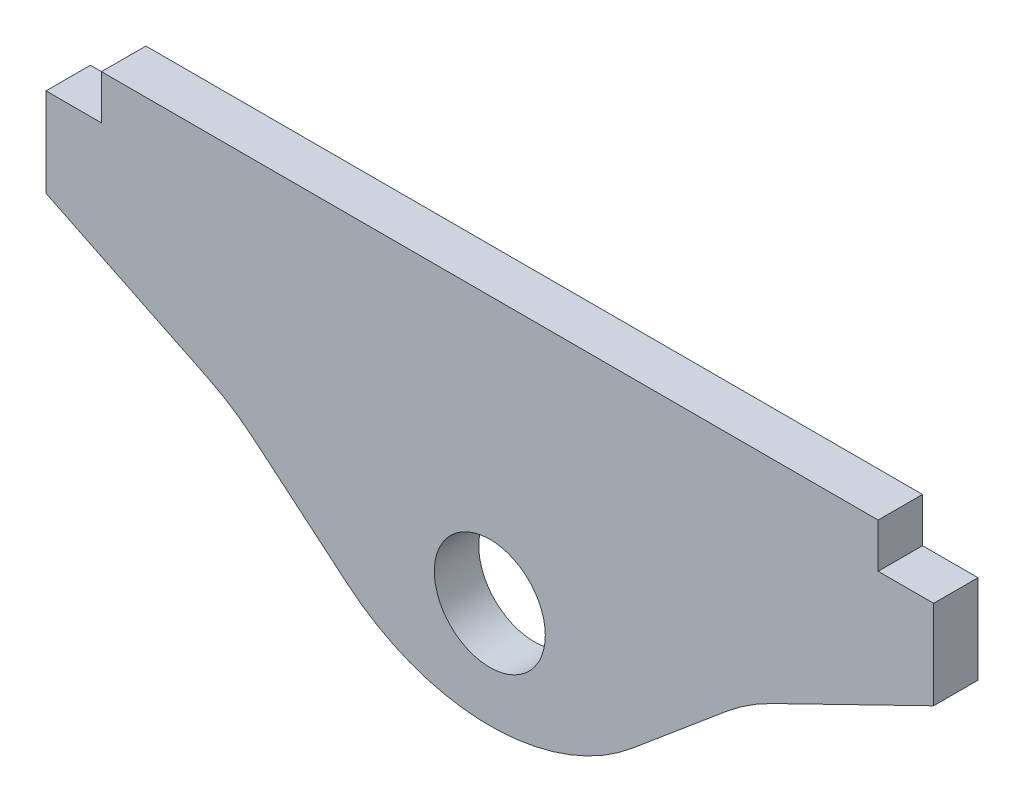
SolidWorks part; units mm, degrees
material "ﾊﾞﾙｻ"
ref_plane "正面" through (0, 0, 0) normal (0, 0, 1) x (1, 0, 0)
ref_plane "平面" through (0, 0, 0) normal (0, 1, 0) x (1, 0, 0)
ref_plane "右側面" through (0, 0, 0) normal (1, 0, 0) x (0, 0, -1)
sketch "ｽｹｯﾁ1" plane through (0, 0, 0) normal (0, 0, 1) x (1, 0, 0)
  line L0 (0, 0) -> (0, 38.4947) construction
  line L1 (0, -7.8324) -> (11.6055, 1.9057)
  line L2 (11.6055, 1.9057) -> (20, 6)
  line L3 (-11.6055, 1.9057) -> (-20, 6)
  line L4 (0, -7.8324) -> (-11.6055, 1.9057)
  line L5 (20, 6) -> (-20, 6)
  line L6 (-20, 6) -> (-20, 10)
  line L7 (-20, 10) -> (-17.5, 10)
  line L8 (-17.5, 10) -> (-17.5, 12)
  line L9 (-17.5, 12) -> (17.5, 12)
  line L10 (20, 10) -> (17.5, 10)
  line L11 (20, 6) -> (20, 10)
  line L12 (17.5, 10) -> (17.5, 12)
  circle A0 centre (0, 0) radius 2.5
  point P8 (0, 6)
  point P16 (0, 12)
  dimension "D3" = 5
  dimension "D1" = 50
  dimension "D2" = 6
  dimension "D4" = 6
  dimension "D5" = 20
  dimension "D6" = 26
  dimension "D7" = 4
  dimension "D8" = 2
  dimension "D9" = 17.5
extrude "ﾎﾞｽ - 押し出し1" add sketch "ｽｹｯﾁ1" along normal blind 2
fillet "ﾌｨﾚｯﾄ1" radius 10 3 edges at (-11.6055, 1.9057, 1) (11.6055, 1.9057, 1) (0, -7.8324, 1)
